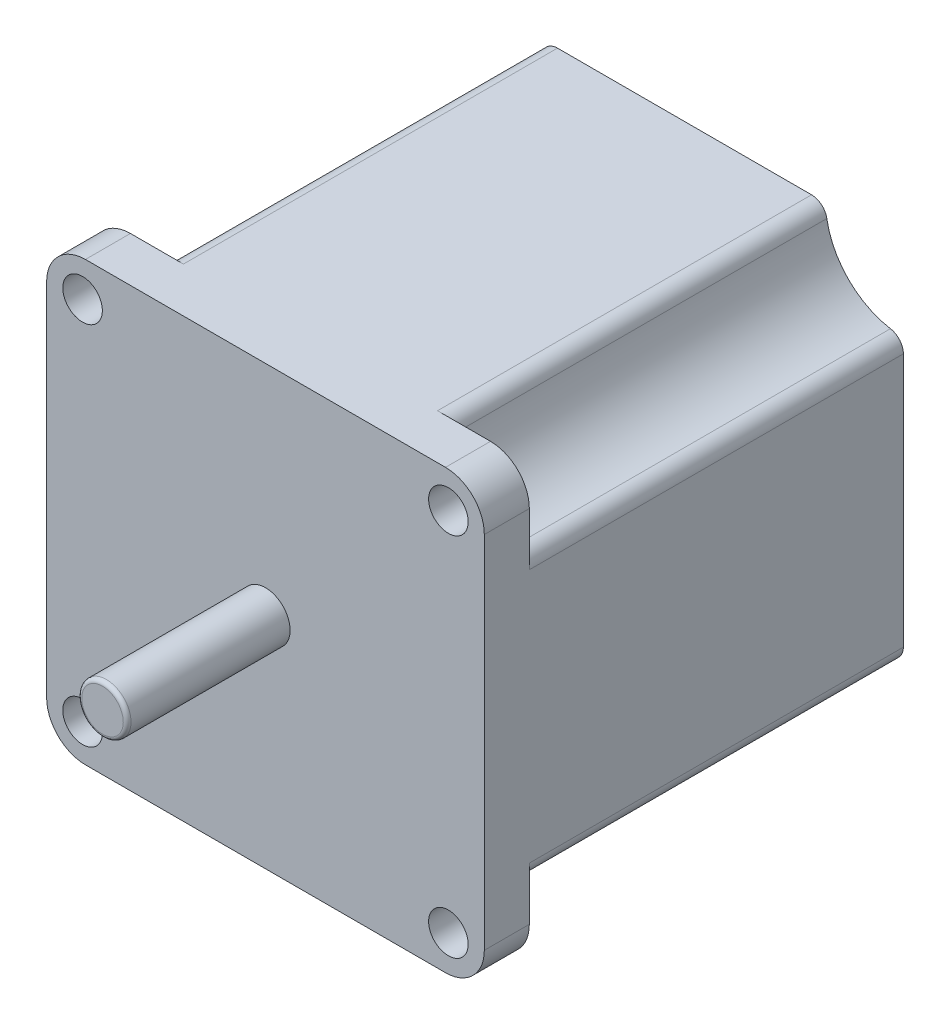
SolidWorks part; units mm, degrees
ref_plane "Plan de face" through (0, 0, 0) normal (0, 0, 1) x (1, 0, 0)
ref_plane "Plan de dessus" through (0, 0, 0) normal (0, 1, 0) x (1, 0, 0)
ref_plane "Plan de droite" through (0, 0, 0) normal (1, 0, 0) x (0, 0, -1)
sketch "Esquisse2" plane through (0, 0, 0) normal (0, 0, 1) x (1, 0, 0)
  line L1 (28.2, 28.2) -> (-28.2, 28.2)
  line L2 (28.2, 28.2) -> (28.2, -28.2)
  line L3 (28.2, -28.2) -> (-28.2, -28.2)
  line L4 (-28.2, 28.2) -> (-28.2, -28.2)
  dimension "D1" = 56.4
  dimension "D2" = 28.2
  dimension "D3" = 56.4
  dimension "D4" = 28.2
extrude "Boss.-Extru.2" add sketch "Esquisse2" along normal blind 54
sketch "Esquisse3" plane through (0, 0, 54) normal (0, 0, 1) x (1, 0, 0)
  line L0 (-28.2, 28.2) -> (-28.2, -28.2) construction
  line L2 (28.2, 28.2) -> (-28.2, 28.2) construction
  circle A0 centre (-23.57, 23.57) radius 2.55
  circle A1 centre (23.57, 23.57) radius 2.55
  circle A2 centre (23.57, -23.57) radius 2.55
  circle A3 centre (-23.57, -23.57) radius 2.55
  point P15 (0, 0)
  dimension "D1" = 5.1
  dimension "D2" = 4.63
  dimension "D3" = 4.63
  dimension "D4" = 4
extrude "Enlèv. mat.-Extru.1" cut sketch "Esquisse3" against normal blind 54
fillet "Congé2" radius 5 1 edges at (28.2, 28.2, 27)
fillet "Congé3" radius 5 1 edges at (28.2, -28.2, 27)
fillet "Congé4" radius 5 1 edges at (-28.2, 28.2, 27)
fillet "Congé6" radius 5 1 edges at (-28.2, -28.2, 27)
sketch "Esquisse4" plane through (0, 0, 0) normal (0, 0, -1) x (-1, 0, 0)
  line L0 (-23.2, 28.2) -> (23.2, 28.2) construction
  line L1 (28.2, 23.2) -> (28.2, -23.2) construction
  line L2 (-28.2, 18.2) -> (-28.2, 28.2)
  line L3 (-28.2, 28.2) -> (-18.2, 28.2)
  line L4 (-28.2, -18.2) -> (-28.2, -28.2)
  line L5 (-28.2, -28.2) -> (-18.2, -28.2)
  line L6 (-18.2, -28.2) -> (-18.4245, -28.2675)
  line L7 (18.2, -28.2) -> (28.2, -28.2)
  line L8 (28.2, -28.2) -> (28.2, -18.2)
  line L9 (28.2, 18.2) -> (28.2, 28.2)
  line L10 (28.2, 28.2) -> (18.2, 28.2)
  arc A0 (18.2, 28.2) -> (28.2, 18.2) centre (28.2, 28.2) ccw
  arc A1 (28.2, -18.2) -> (18.2, -28.2) centre (28.2, -28.2) ccw
  arc A2 (-18.2, -28.2) -> (-28.2, -18.2) centre (-28.2, -28.2) ccw
  arc A3 (-28.2, 18.2) -> (-18.2, 28.2) centre (-28.2, 28.2) ccw
  point P19 (0, 0)
  circle M8 centre (-23.57, -23.57) radius 2.55
  line M11 (-23.2, -28.2) -> (23.2, -28.2)
  line M17 (-28.2, 23.2) -> (-28.2, -23.2)
  arc M18 (-28.2, -23.2) -> (-23.2, -28.2) centre (-23.2, -23.2) ccw
  dimension "D1" = 0
  dimension "D2" = 10
  dimension "D3" = 10
  dimension "D4" = 4
extrude "Enlèv. mat.-Extru.2" cut sketch "Esquisse4" against normal blind 48.2 contours A2 M11 M17 M18 M8 | L3 A3 L2 | A1 L7 L8 | A0 L9 L10
fillet "Congé7" radius 2 1 edges at (18.2, 28.2, 24.1)
fillet "Congé8" radius 2 1 edges at (28.2, 18.2, 24.1)
fillet "Congé9" radius 2 1 edges at (-18.2, 28.2, 24.1)
fillet "Congé10" radius 2 1 edges at (-28.2, 18.2, 24.1)
fillet "Congé11" radius 2 1 edges at (-28.2, -18.2, 24.1)
fillet "Congé12" radius 2 1 edges at (-18.2, -28.2, 24.1)
fillet "Congé13" radius 2 1 edges at (18.2, -28.2, 24.1)
fillet "Congé14" radius 2 1 edges at (28.2, -18.2, 24.1)
sketch "Esquisse5" plane through (0, 0, 54) normal (0, 0, 1) x (1, 0, 0)
  circle A0 centre (0, 0) radius 3.175
  dimension "D1" = 6.35
extrude "Boss.-Extru.3" add sketch "Esquisse5" along normal blind 21
fillet "Congé15" radius 0.5 1 edges at (3.175, 0, 75)
